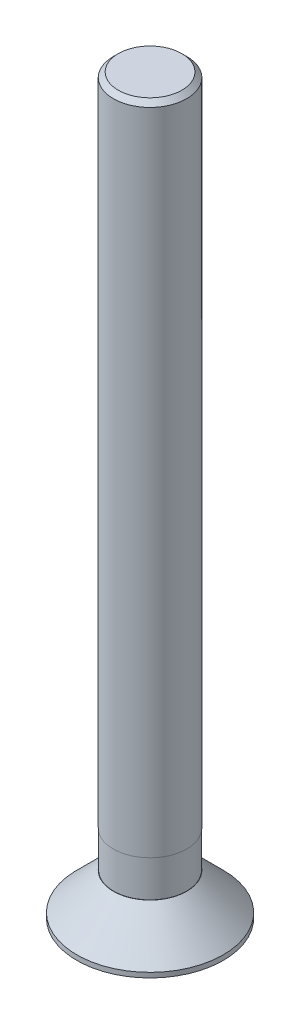
SolidWorks part; units mm, degrees
material "AISI 304"
ref_plane "Front Plane" through (0, 0, 0) normal (0, 0, 1) x (1, 0, 0)
ref_plane "Top Plane" through (0, 0, 0) normal (0, 1, 0) x (1, 0, 0)
ref_plane "Right Plane" through (0, 0, 0) normal (1, 0, 0) x (0, 0, -1)
sketch "Sketch1" plane through (0, 0, 0) normal (0, 0, 1) x (1, 0, 0)
  line L0 (0, 0) -> (0, 13.3573) construction
  line L1 (0, -1.8739) -> (-3, -1.8739)
  line L2 (-3, -1.8739) -> (-3, -1.6739)
  line L3 (-1.5, 28.1261) -> (0, 28.1261)
  line L4 (-1.5, 1.3261) -> (-1.5, 28.1261)
  line L5 (-3, -1.6739) -> (-1.5, -0.1739)
  line L7 (0, -1.8739) -> (0, 28.1261)
  line L8 (-1.5, 1.3261) -> (-1.49, 1.3261)
  line L10 (-1.5, -0.1739) -> (-1.49, -0.1739)
  line L18 (-1.49, -0.1739) -> (-1.49, 1.3261)
  point P9 (-1.5, 9.9261)
  point P12 (-1.49, 3.622)
  point P13 (-1.49, 9.9161)
  point P16 (0, 3.6361)
  dimension "dk" = 6
  dimension "c" = 0.2
  dimension "k" = 1.7
  dimension "d" = 3
  dimension "l" = 30
  dimension "lg" = 3.2
revolve "Revolve1" add sketch "Sketch1" angle 360 about L0
chamfer "Chamfer1" distance 0.2 angle 45 1 edges at (0, 28.1261, -1.5)
sketch "Sketch2" plane through (0, -1.8739, 0) normal (0, -1, 0) x (1, 0, 0)
  line L1 (1.1547, 0) -> (0.5774, 1)
  line L2 (0.5774, 1) -> (-0.5774, 1)
  line L3 (-0.5774, 1) -> (-1.1547, 0)
  line L4 (-1.1547, 0) -> (-0.5774, -1)
  line L5 (-0.5774, -1) -> (0.5774, -1)
  line L6 (0.5774, -1) -> (1.1547, 0)
  circle A0 centre (0, 0) radius 1 construction
  dimension "s" = 2
extrude "hex depth" cut sketch "Sketch2" against normal blind 1.2
sketch "Sketch3" plane through (0, -1.8739, 0) normal (0, -1, 0) x (1, 0, 0)
  circle A0 centre (0, 0) radius 1.1547
ref_plane "Plane1" through (0, -1.6739, 0) normal (0, 1, 0) x (1, 0, 0)
sketch "Sketch4" plane through (0, -1.6739, 0) normal (0, 1, 0) x (1, 0, 0)
  line L0 (-0.5774, -1) -> (-1.1547, 0) construction
  circle A0 centre (0, 0) radius 1
loft "hex corner cut" cut profiles "Sketch4", "Sketch3"
thread "thread M3" [suppressed] pitch 0.6 start angle 0, offset 0, length 0, pitch 0.6, diameter 3
ref_plane "Plane3" [suppressed] through (1.5, 1.3261, 0) normal (0, 0, 1) x (1, 0, 0)
sketch "Thread Profile2" [suppressed] plane through (1.5, 1.3261, 0) normal (0, 0, 1) x (1, 0, 0)
  line L0 (0, 0) -> (0, 0.6) construction
  line L11 (0, 0) -> (0, 0.525)
  line L12 (0, 0.525) -> (-0.3248, 0.3375)
  line L13 (-0.3248, 0.3375) -> (-0.3248, 0.1875)
  line L15 (-0.3248, 0.1875) -> (0, 0)
  line L17 (-0.3248, 0.2625) -> (0, 0.2625) construction
  point P2 (0, 0)
  dimension "Pitch" = 0.6
  dimension "Profile_Angle" = 60
  dimension "Profile_Land" = 0.15
  dimension "Profile_Height" = 0.3248
thread "Thread M4" [suppressed] pitch 0.7 start angle 0, offset 0.01, length 0, pitch 0.7, diameter 4
ref_plane "Plane4" [suppressed] through (2, 19.1361, 0) normal (0, 0, 1) x (1, 0, 0)
sketch "Thread Profile3" [suppressed] plane through (2, 19.1361, 0) normal (0, 0, 1) x (1, 0, 0)
  line L0 (0, 0) -> (0, 0.7) construction
  line L11 (0, 0) -> (0, 0.6125)
  line L12 (0, 0.6125) -> (-0.3789, 0.3937)
  line L13 (-0.3789, 0.3937) -> (-0.3789, 0.2187)
  line L15 (-0.3789, 0.2187) -> (0, 0)
  line L17 (-0.3789, 0.3062) -> (0, 0.3062) construction
  point P2 (0, 0)
  dimension "Pitch" = 0.7
  dimension "Profile_Angle" = 60
  dimension "Profile_Land" = 0.175
  dimension "Profile_Height" = 0.3789
thread "Thread M5" [suppressed] pitch 0.8 start angle 0, offset 0.01, length 0, pitch 0.8, diameter 5
ref_plane "Plane5" [suppressed] through (2.5, 32.1361, 0) normal (0, 0, 1) x (1, 0, 0)
sketch "Thread Profile4" [suppressed] plane through (2.5, 32.1361, 0) normal (0, 0, 1) x (1, 0, 0)
  line L0 (0, 0) -> (0, 0.8) construction
  line L11 (0, 0) -> (0, 0.7)
  line L12 (0, 0.7) -> (-0.433, 0.45)
  line L13 (-0.433, 0.45) -> (-0.433, 0.25)
  line L15 (-0.433, 0.25) -> (0, 0)
  line L17 (-0.433, 0.35) -> (0, 0.35) construction
  point P2 (0, 0)
  dimension "Pitch" = 0.8
  dimension "Profile_Angle" = 60
  dimension "Profile_Land" = 0.2
  dimension "Profile_Height" = 0.433
thread "Thread M6" [suppressed] pitch 1 start angle 0, offset 0.1, length 0, pitch 1, diameter 6
ref_plane "Plane8" [suppressed] through (3, 4.5261, 0) normal (0, 0, 1) x (1, 0, 0)
sketch "Thread Profile7" [suppressed] plane through (3, 4.5261, 0) normal (0, 0, 1) x (1, 0, 0)
  line L0 (0, 0) -> (0, 1) construction
  line L11 (0, 0) -> (0, 0.875)
  line L12 (0, 0.875) -> (-0.5413, 0.5625)
  line L13 (-0.5413, 0.5625) -> (-0.5413, 0.3125)
  line L15 (-0.5413, 0.3125) -> (0, 0)
  line L17 (-0.5413, 0.4375) -> (0, 0.4375) construction
  point P2 (0, 0)
  dimension "Pitch" = 1
  dimension "Profile_Angle" = 60
  dimension "Profile_Land" = 0.25
  dimension "Profile_Height" = 0.5413
thread "Thread M8" [suppressed] pitch 1.25 start angle 0, offset 0.1, length 0, pitch 1.25, diameter 8
ref_plane "Plane6" [suppressed] through (4, 6.4261, 0) normal (0, 0, 1) x (1, 0, 0)
sketch "Thread Profile5" [suppressed] plane through (4, 6.4261, 0) normal (0, 0, 1) x (1, 0, 0)
  line L0 (0, 0) -> (0, 1.25) construction
  line L11 (0, 0) -> (0, 1.0937)
  line L12 (0, 1.0937) -> (-0.6766, 0.7031)
  line L13 (-0.6766, 0.7031) -> (-0.6766, 0.3906)
  line L15 (-0.6766, 0.3906) -> (0, 0)
  line L17 (-0.6766, 0.5469) -> (0, 0.5469) construction
  point P2 (0, 0)
  dimension "Pitch" = 1.25
  dimension "Profile_Angle" = 60
  dimension "Profile_Land" = 0.3125
  dimension "Profile_Height" = 0.6766
thread "Thread M10" [suppressed] pitch 1.5 start angle 0, offset 0.1, length 0, pitch 1.5, diameter 10
ref_plane "Plane7" [suppressed] through (5, 3.8261, 0) normal (0, 0, 1) x (1, 0, 0)
sketch "Thread Profile6" [suppressed] plane through (5, 3.8261, 0) normal (0, 0, 1) x (1, 0, 0)
  line L0 (0, 0) -> (0, 1.5) construction
  line L11 (0, 0) -> (0, 1.3125)
  line L12 (0, 1.3125) -> (-0.8119, 0.8437)
  line L13 (-0.8119, 0.8437) -> (-0.8119, 0.4687)
  line L15 (-0.8119, 0.4687) -> (0, 0)
  line L17 (-0.8119, 0.6562) -> (0, 0.6562) construction
  point P2 (0, 0)
  dimension "Pitch" = 1.5
  dimension "Profile_Angle" = 60
  dimension "Profile_Land" = 0.375
  dimension "Profile_Height" = 0.8119
thread "Thread M12" [suppressed] pitch 1.75 start angle 0, offset 0.1, length 0, pitch 1.75, diameter 12
ref_plane "Plane9" [suppressed] through (6, 10.0261, 0) normal (0, 0, 1) x (1, 0, 0)
sketch "Thread Profile8" [suppressed] plane through (6, 10.0261, 0) normal (0, 0, 1) x (1, 0, 0)
  line L0 (0, 0) -> (0, 1.75) construction
  line L11 (0, 0) -> (0, 1.5312)
  line L12 (0, 1.5312) -> (-0.9472, 0.9844)
  line L13 (-0.9472, 0.9844) -> (-0.9472, 0.5469)
  line L15 (-0.9472, 0.5469) -> (0, 0)
  line L17 (-0.9472, 0.7656) -> (0, 0.7656) construction
  point P2 (0, 0)
  dimension "Pitch" = 1.75
  dimension "Profile_Angle" = 60
  dimension "Profile_Land" = 0.4375
  dimension "Profile_Height" = 0.9472
thread "Thread M14" [suppressed] pitch 2 start angle 0, offset 0.1, length 0, pitch 2, diameter 14
ref_plane "Plane10" [suppressed] through (7, 11.2261, 0) normal (0, 0, 1) x (1, 0, 0)
sketch "Thread Profile9" [suppressed] plane through (7, 11.2261, 0) normal (0, 0, 1) x (1, 0, 0)
  line L0 (0, 0) -> (0, 2) construction
  line L11 (0, 0) -> (0, 1.75)
  line L12 (0, 1.75) -> (-1.0825, 1.125)
  line L13 (-1.0825, 1.125) -> (-1.0825, 0.625)
  line L15 (-1.0825, 0.625) -> (0, 0)
  line L17 (-1.0825, 0.875) -> (0, 0.875) construction
  point P2 (0, 0)
  dimension "Pitch" = 2
  dimension "Profile_Angle" = 60
  dimension "Profile_Land" = 0.5
  dimension "Profile_Height" = 1.0825
thread "Thread M16" [suppressed] pitch 2 start angle 0, offset 0.1, length 0, pitch 2, diameter 16
ref_plane "Plane11" [suppressed] through (8, 11.7261, 0) normal (0, 0, 1) x (1, 0, 0)
sketch "Thread Profile10" [suppressed] plane through (8, 11.7261, 0) normal (0, 0, 1) x (1, 0, 0)
  line L0 (0, 0) -> (0, 2) construction
  line L11 (0, 0) -> (0, 1.75)
  line L12 (0, 1.75) -> (-1.0825, 1.125)
  line L13 (-1.0825, 1.125) -> (-1.0825, 0.625)
  line L15 (-1.0825, 0.625) -> (0, 0)
  line L17 (-1.0825, 0.875) -> (0, 0.875) construction
  point P2 (0, 0)
  dimension "Pitch" = 2
  dimension "Profile_Angle" = 60
  dimension "Profile_Land" = 0.5
  dimension "Profile_Height" = 1.0825
thread "Thread M18" [suppressed] pitch 2.5 start angle 0, offset 0.1, length 0, pitch 2.5, diameter 18
ref_plane "Plane12" [suppressed] through (9, 13.7261, 0) normal (0, 0, 1) x (1, 0, 0)
sketch "Thread Profile11" [suppressed] plane through (9, 13.7261, 0) normal (0, 0, 1) x (1, 0, 0)
  line L0 (0, 0) -> (0, 2.5) construction
  line L11 (0, 0) -> (0, 2.1875)
  line L12 (0, 2.1875) -> (-1.3532, 1.4062)
  line L13 (-1.3532, 1.4062) -> (-1.3532, 0.7812)
  line L15 (-1.3532, 0.7812) -> (0, 0)
  line L17 (-1.3532, 1.0937) -> (0, 1.0937) construction
  point P2 (0, 0)
  dimension "Pitch" = 2.5
  dimension "Profile_Angle" = 60
  dimension "Profile_Land" = 0.625
  dimension "Profile_Height" = 1.3532
thread "Thread M20" [suppressed] pitch 2.5 start angle 0, offset 0.1, length 0, pitch 2.5, diameter 20
ref_plane "Plane13" [suppressed] through (10, 6.8261, 0) normal (0, 0, 1) x (1, 0, 0)
sketch "Thread Profile12" [suppressed] plane through (10, 6.8261, 0) normal (0, 0, 1) x (1, 0, 0)
  line L0 (0, 0) -> (0, 2.5) construction
  line L11 (0, 0) -> (0, 2.1875)
  line L12 (0, 2.1875) -> (-1.3532, 1.4062)
  line L13 (-1.3532, 1.4062) -> (-1.3532, 0.7812)
  line L15 (-1.3532, 0.7812) -> (0, 0)
  line L17 (-1.3532, 1.0937) -> (0, 1.0937) construction
  point P2 (0, 0)
  dimension "Pitch" = 2.5
  dimension "Profile_Angle" = 60
  dimension "Profile_Land" = 0.625
  dimension "Profile_Height" = 1.3532
thread "Thread M22" [suppressed] pitch 2.5 start angle 0, offset 0.1, length 0, pitch 2.5, diameter 22
ref_plane "Plane14" [suppressed] through (11, 18.8261, 0) normal (0, 0, 1) x (1, 0, 0)
sketch "Thread Profile13" [suppressed] plane through (11, 18.8261, 0) normal (0, 0, 1) x (1, 0, 0)
  line L0 (0, 0) -> (0, 2.5) construction
  line L11 (0, 0) -> (0, 2.1875)
  line L12 (0, 2.1875) -> (-1.3532, 1.4062)
  line L13 (-1.3532, 1.4062) -> (-1.3532, 0.7812)
  line L15 (-1.3532, 0.7812) -> (0, 0)
  line L17 (-1.3532, 1.0937) -> (0, 1.0937) construction
  point P2 (0, 0)
  dimension "Pitch" = 2.5
  dimension "Profile_Angle" = 60
  dimension "Profile_Land" = 0.625
  dimension "Profile_Height" = 1.3532
thread "Thread M24" [suppressed] pitch 3 start angle 0, offset 0.1, length 0, pitch 3, diameter 24
ref_plane "Plane15" [suppressed] through (12, 12.3261, 0) normal (0, 0, 1) x (1, 0, 0)
sketch "Thread Profile14" [suppressed] plane through (12, 12.3261, 0) normal (0, 0, 1) x (1, 0, 0)
  line L0 (0, 0) -> (0, 3) construction
  line L11 (0, 0) -> (0, 2.625)
  line L12 (0, 2.625) -> (-1.6238, 1.6875)
  line L13 (-1.6238, 1.6875) -> (-1.6238, 0.9375)
  line L15 (-1.6238, 0.9375) -> (0, 0)
  line L17 (-1.6238, 1.3125) -> (0, 1.3125) construction
  point P2 (0, 0)
  dimension "Pitch" = 3
  dimension "Profile_Angle" = 60
  dimension "Profile_Land" = 0.75
  dimension "Profile_Height" = 1.6238
